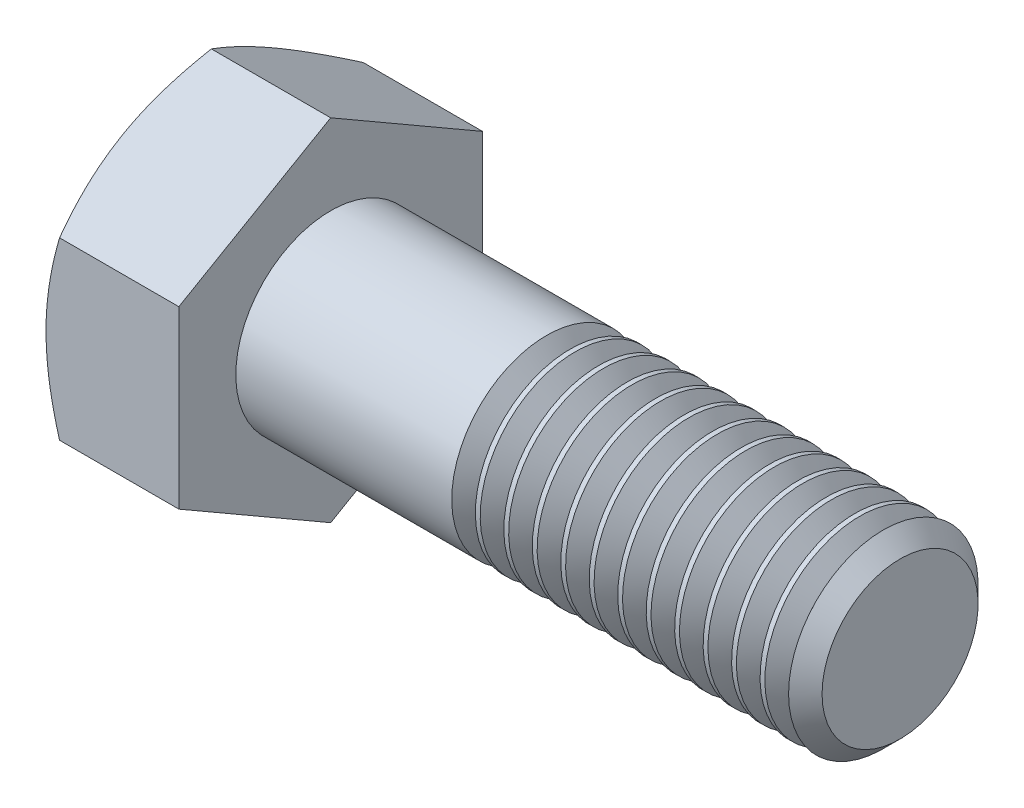
SolidWorks part; units mm, degrees
ref_plane "Plane1" through (0, 0, 0) normal (0, 0, 1) x (1, 0, 0)
ref_plane "Plane2" through (0, 0, 0) normal (0, 1, 0) x (1, 0, 0)
ref_plane "Plane3" through (0, 0, 0) normal (1, 0, 0) x (0, 0, -1)
sketch "Sketch1" plane through (0, 0, 0) normal (1, 0, 0) x (0, 0, -1)
  line L0 (4, 2.3094) -> (4, -2.3094)
  line L1 (-4, 2.3094) -> (-4, -2.3094)
  line L2 (4, -2.3094) -> (0, -4.6188)
  line L3 (0, -4.6188) -> (-4, -2.3094)
  line L4 (4, 2.3094) -> (0, 4.6188)
  line L5 (0, 4.6188) -> (-4, 2.3094)
  dimension "Width_flats" = 8
  dimension "D2" = 120
  dimension "D3" = 4
  dimension "D4" = 4
  dimension "D5" = 4
extrude "BaseHead" add sketch "Sketch1" along normal blind 3.5
sketch "BodySke" plane through (0, 0, 0) normal (0, 0, 1) x (1, 0, 0)
  line L1 (0, 0) -> (18.5, 0)
  line L2 (0, 0) -> (0, 2.5)
  line L4 (18.5, 0) -> (18.5, 2.055)
  line L5 (3.5, 4.6188) -> (3.5, 2.3094) construction
  line L6 (18.5, 2.055) -> (18.055, 2.5)
  line L7 (0, 0) -> (110.49, 0) construction
  line L8 (18.5, -2.055) -> (18.055, -2.5) construction
  line L9 (0, 2.3094) -> (0, -2.3094) construction
  line L10 (4.3, 15.24) -> (4.3, -1.27) construction
  line L11 (9.5, 15.24) -> (9.5, -1.27) construction
  line L12 (3.5, 2.3094) -> (3.5, -2.3094) construction
  line L15 (0, 2.5) -> (18.055, 2.5)
  dimension "Length" = 15
  dimension "Body_ch_ang" = 45
  dimension "Diameter" = 5
  dimension "Minor_dia" = 4.11
  dimension "Advance" = 0.8
  dimension "Thread_nom" = 9
revolve "BaseBody" add sketch "BodySke" angle 360 about L7
cosmetic thread "ThreadCosmetic" [suppressed] parameters "Thread_length"=9, "Thread_minor"=4.11
fillet "HeadFillet" [suppressed] radius 0.2
sketch "Sketch3" plane through (0, 0, 0) normal (0, 0, 1) x (1, 0, 0)
  line L0 (0, 4) -> (3.244, 9.6188)
  line L1 (0, 4.6188) -> (0, 2.3094) construction
  line L2 (3.244, 9.6188) -> (3.244, 14.6188)
  line L3 (3.244, 14.6188) -> (-10, 14.6188)
  line L4 (-10, 14.6188) -> (-10, 4)
  line L5 (-10, 4) -> (0, 4)
  line L6 (0, 0) -> (99.06, 0) construction
  line L7 (3.5, 4.6188) -> (0, 4.6188) construction
  dimension "D1" = 4
  dimension "D2" = 5
  dimension "D3" = 10
  dimension "D4" = 5
  dimension "Head_ch_ang" = 30
revolve "HeadChamfer" cut sketch "Sketch3" angle 360 about L6
sketch "ThdSchSke" plane through (0, 0, 0) normal (0, 0, 1) x (1, 0, 0)
  line L0 (9.5, -2.055) -> (9.1884, -2.5)
  line L1 (9.5, -2.055) -> (9.8116, -2.5)
  line L2 (9.8116, -2.5) -> (9.8116, -3.125)
  line L3 (-3.175, 0) -> (5.1513, 0) construction
  line L5 (9.8116, -3.125) -> (9.1884, -3.125)
  line L6 (9.1884, -3.125) -> (9.1884, -2.5)
  dimension "Thread_minor" = 4.11
  dimension "Diameter" = 5
  dimension "Start" = 9.5
  dimension "SideAngle" = 55
  dimension "VeeAngle" = 70
  dimension "Overcut" = 6.25
revolve "ThreadSchematic" cut sketch "ThdSchSke" angle 360 about L3
pattern_linear "ThdSchPat" count 12 spacing 0.75 along (1, 0, 0) of "ThreadSchematic"
equation "\"D3@Sketch1\" = \"Width_flats@Sketch1\" / 2"
equation "\"D4@Sketch1\" = \"D3@Sketch1\""
equation "\"D5@Sketch1\" = \"D4@Sketch1\""
equation "\"Thread_minor@ThreadCosmetic\" = \"Minor_dia@BodySke\""
equation "\"D1@Sketch3\" = \"Width_flats@Sketch1\" / 2"
equation "\"Thread_length@ThreadCosmetic\" = ((sgn( (\"Length@BodySke\" - \"Advance@BodySke\" ) - \"Thread_nom@BodySke\" )-1)*( (\"Length@BodySke\" - \"Advance@BodySke\" ) - \"Thread_nom@BodySke\" ))/-2+ \"Thread_nom@BodySke\""
equation "\"Thread_minor@ThdSchSke\" = \"Minor_dia@BodySke\""
equation "\"Diameter@ThdSchSke\" = \"Diameter@BodySke\""
equation "\"Overcut@ThdSchSke\" = \"Diameter@BodySke\" * 1.25"
equation "\"Start@ThdSchSke\" = \"Head_ht@BaseHead\" + \"Length@BodySke\" - \"Thread_length@ThreadCosmetic\"  '---Non-countersunk---"
equation "\"Num_threads@ThdSchPat\" = int( \"Thread_length@ThreadCosmetic\" / \"Advance@BodySke\" + 0.999 )  + 1"
equation "\"Advance@ThdSchPat\" = \"Thread_length@ThreadCosmetic\" /  (\"Num_threads@ThdSchPat\" - 1) 'relax it"
equation "\"Num_threads@ThdSchPat\" = \"Num_threads@ThdSchPat\" - sgn( \"Num_threads@ThdSchPat\" - 1) '---chamfered tips only---"
